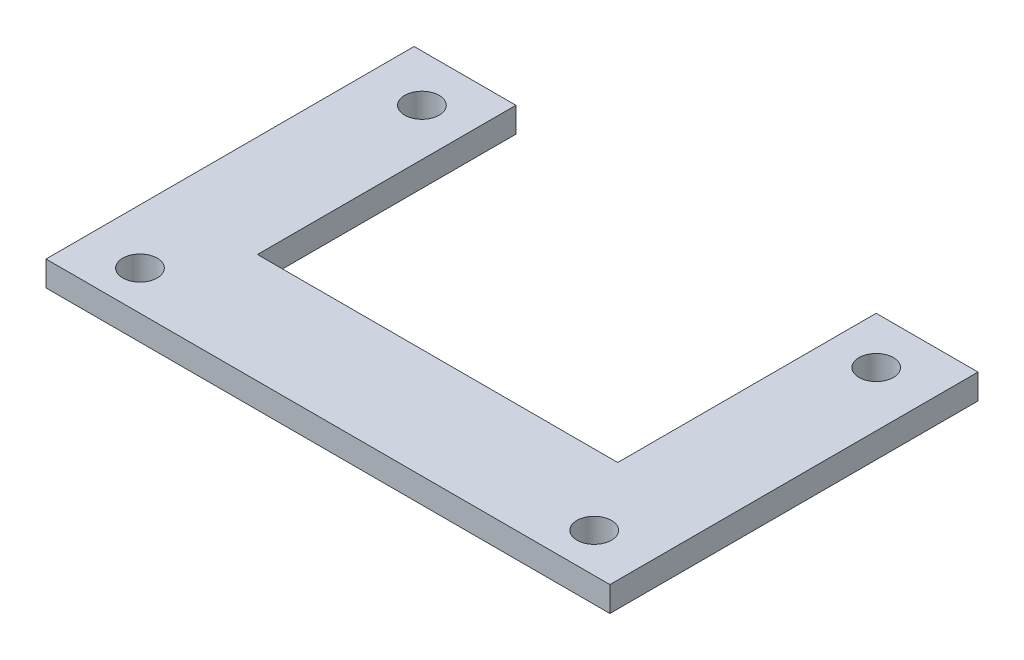
SolidWorks part; units mm, degrees
ref_plane "前视基准面" through (0, 0, 0) normal (0, 0, 1) x (1, 0, 0)
ref_plane "上视基准面" through (0, 0, 0) normal (0, 1, 0) x (1, 0, 0)
ref_plane "右视基准面" through (0, 0, 0) normal (1, 0, 0) x (0, 0, -1)
sketch "草图1" plane through (0, 0, 0) normal (0, 1, 0) x (1, 0, 0)
  line L1 (0, 0) -> (36, 0)
  line L2 (0, 0) -> (0, -24)
  line L3 (0, -24) -> (36, -24)
  line L4 (36, 0) -> (36, -24)
  dimension "D1" = 36
  dimension "D2" = 24
extrude "凸台-拉伸3" add sketch "草图1" along normal blind 1.6
sketch "草图3" plane through (0, 1.6, 0) normal (0, 1, 0) x (1, 0, 0)
  line L0 (36, 0) -> (0, 0) construction
  line L1 (7, 0) -> (29, 0)
  line L2 (7, 0) -> (7, -16)
  line L3 (7, -16) -> (29, -16)
  line L4 (29, 0) -> (29, -16)
  line L5 (0, 0) -> (0, -24) construction
  line L6 (36, -24) -> (36, 0) construction
  line L7 (0, -24) -> (36, -24) construction
  dimension "D1" = 7
  dimension "D2" = 7
  dimension "D3" = 8
extrude "切除-拉伸1" cut sketch "草图3" against normal blind 1.6
sketch "草图4" plane through (0, 1.6, 0) normal (0, 1, 0) x (1, 0, 0)
  line L0 (3.5, -3) -> (32.5, -3) construction
  line L1 (32.5, -3) -> (32.5, -21) construction
  line L2 (32.5, -21) -> (3.5, -21) construction
  line L3 (3.5, -21) -> (3.5, -3) construction
  line L4 (3.5, -3) -> (3.5, 0) construction
  line L5 (7, 0) -> (0, 0) construction
  line L6 (0, -24) -> (36, -24) construction
  line L7 (32.5, -3) -> (32.5, 0) construction
  line L8 (36, 0) -> (29, 0) construction
  circle A0 centre (3.5, -3) radius 1.1
  circle A1 centre (32.5, -3) radius 1.1
  circle A2 centre (3.5, -21) radius 1.1
  circle A3 centre (32.5, -21) radius 1.1
  dimension "D1" = 2.2
  dimension "D2" = 3
  dimension "D3" = 3
extrude "切除-拉伸2" cut sketch "草图4" against normal blind 1.6
sketch "草图5" plane through (0, 1.6, 0) normal (0, 1, 0) x (1, 0, 0)
  line L0 (7, 0) -> (6.5, 0)
  line L1 (7, 0) -> (0, 0) construction
  line L2 (6.5, 0) -> (6.5, -16.5)
  line L3 (6.5, -16.5) -> (29.5, -16.5)
  line L4 (29.5, -16.5) -> (29.5, 0)
  line L5 (36, 0) -> (29, 0) construction
  line L6 (29.5, 0) -> (29, 0)
  line L7 (29, 0) -> (29, -16)
  line L8 (29, -16) -> (7, -16)
  line L9 (7, -16) -> (7, 0)
  dimension "D1" = 0.5
  dimension "D2" = 0.5
  dimension "D3" = 0.5
extrude "切除-拉伸3" cut sketch "草图5" against normal blind 3
sketch "草图6" plane through (0, 1.6, 0) normal (0, 1, 0) x (1, 0, 0)
  line L0 (36, -24) -> (36, 0) construction
  line L1 (0, -24) -> (36, -24)
  line L2 (0, -24) -> (0, -23.5)
  line L3 (0, -23.5) -> (36, -23.5)
  line L4 (36, -24) -> (36, -23.5)
  dimension "D1" = 0.5
extrude "切除-拉伸4" cut sketch "草图6" against normal blind 3
